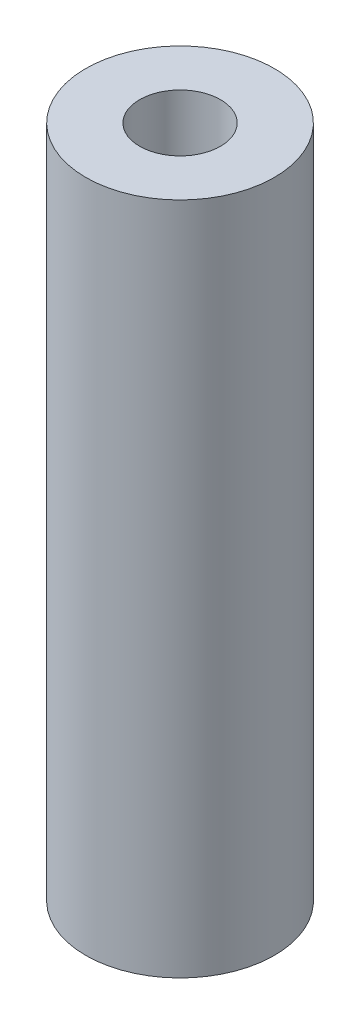
SolidWorks part; units mm, degrees
ref_plane "Спереди" through (0, 0, 0) normal (0, 0, 1) x (1, 0, 0)
ref_plane "Сверху" through (0, 0, 0) normal (0, 1, 0) x (1, 0, 0)
ref_plane "Справа" through (0, 0, 0) normal (1, 0, 0) x (0, 0, -1)
other "Configuration Table"
sketch "Эскиз1" plane through (0, 0, 0) normal (0, 1, 0) x (1, 0, 0)
  circle A0 centre (-2.2931, 1.3427) radius 3.5
  circle A1 centre (-2.2931, 1.3427) radius 1.5
  dimension "D1" = 7
  dimension "D2" = 3
  dimension "D3" = 0
extrude "Бобышка-Вытянуть1" add sketch "Эскиз1" along normal blind 25
